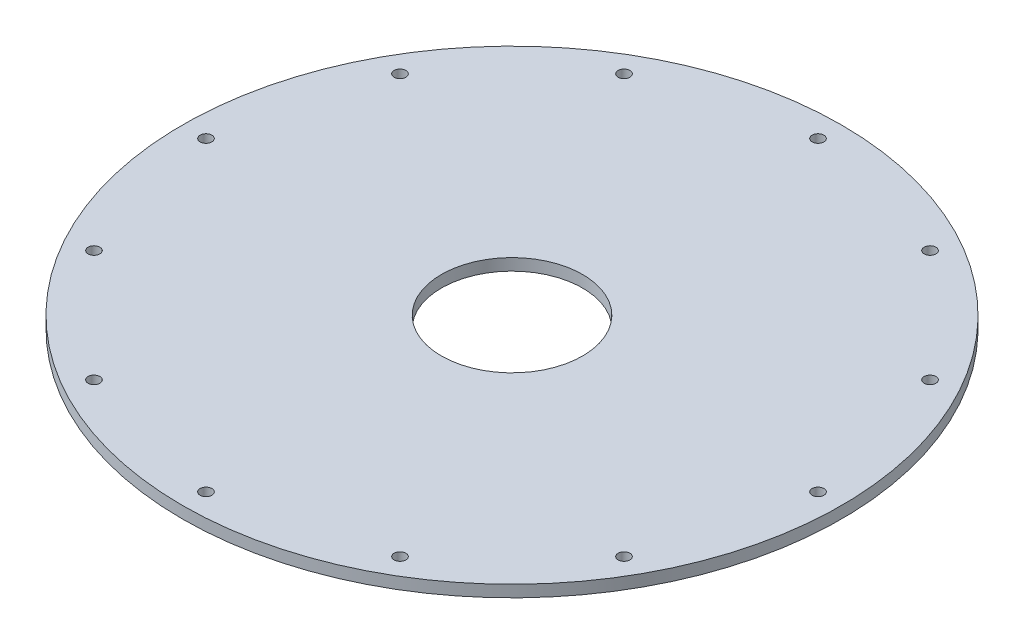
SolidWorks part; units mm, degrees
material "6063-T6"
ref_plane "Front Plane" through (0, 0, 0) normal (0, 0, 1) x (1, 0, 0)
ref_plane "Top Plane" through (0, 0, 0) normal (0, 1, 0) x (1, 0, 0)
ref_plane "Right Plane" through (0, 0, 0) normal (1, 0, 0) x (0, 0, -1)
ref_axis "Axis1" through (0, 55, 0) along (0, -1, 0)
sketch "Sketch1" plane through (0, 0, 0) normal (0, 0, 1) x (1, 0, 0)
  line L0 (-44.45, 0) -> (-9.525, 0)
  line L1 (0, 55) -> (0, -55) construction
  line L2 (-44.45, 0) -> (-44.45, 1.5875)
  line L3 (-44.45, 1.5875) -> (-9.525, 1.5875)
  line L4 (-44.45, 1.5875) -> (-9.525, 1.5875) construction
  line L5 (-9.525, 1.5875) -> (-9.525, 0)
  line L6 (-9.525, 0) -> (0, 0) construction
  line L7 (-44.45, 0) -> (-44.45, 1.5875) construction
  line L8 (-9.525, 1.5875) -> (-9.525, 0) construction
revolve "Revolve1" add sketch "Sketch1" angle 360 about axis through (0, 55, 0) along (0, -1, 0)
ref_plane "Hole Location Plane" through (0, 3.175, 0) normal (0, 1, 0) x (1, 0, 0)
sketch "Hole Location" plane through (0, 3.175, 0) normal (0, 1, 0) x (1, 0, 0)
  line L0 (0, 0) -> (-41.275, 0) construction
  circle A0 centre (0, 0) radius 41.275 construction
  dimension "D1" = 82.55
hole_wizard "1/16 (0.0625) Diameter Hole1" positions "Sketch4" profile "Sketch5" hole size "1/16" standard "ANSI Inch" end condition through all
sketch "Sketch4" plane through (0, 1.5875, 0) normal (0, 1, 0) x (1, 0, 0)
  point P0 (-41.275, 0)
sketch "Sketch5" plane through (-41.275, 1.5875, 0) normal (1, 0, 0) x (0, 0, 1)
  line L0 (0, 0) -> (0, 1.5875)
  line L1 (0, 1.5875) -> (0.7937, 1.5875)
  line L2 (0.7937, 1.5875) -> (0.7937, 0)
  line L5 (0.7937, 0) -> (0, 0)
  line L11 (0, -6.35) -> (0, 107.95) construction
  dimension "Thru Hole Dia." = 1.5875
  dimension "Thru Hole Depth" = 1.5875
pattern_circular "CirPattern1" count 12 every 30 about axis through (0, 0, 0) along (0, 1, 0) of "1/16 (0.0625) Diameter Hole1"
equation "\"D1@Hole Location\"=\"TANK DIAMETER@Cryo Tank.Assembly\"+\"GASKET SEAT THICKNESS@Cryo Tank.Assembly\""
